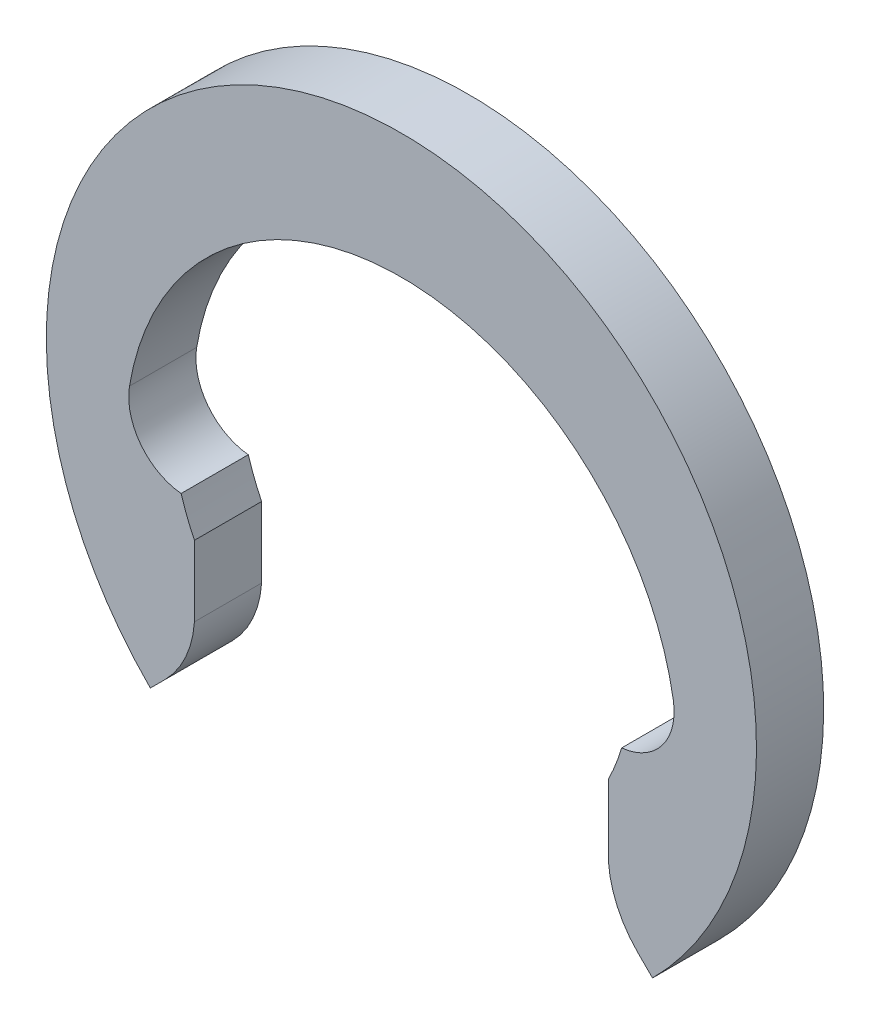
SolidWorks part; units mm, degrees
ref_plane "Front" through (0, 0, 0) normal (0, 0, 1) x (1, 0, 0)
ref_plane "Top" through (0, 0, 0) normal (0, 1, 0) x (1, 0, 0)
ref_plane "Right" through (0, 0, 0) normal (1, 0, 0) x (0, 0, -1)
sketch "Layout" plane through (0, 0, 0) normal (0, 0, 1) x (1, 0, 0)
  line L0 (0, 3.7) -> (0, -3.7) construction
  line L1 (-2.4, 0) -> (-2.8333, 0) construction
  line L2 (-3.7, 0) -> (-4.4, 0) construction
  line L3 (-2.4, 0) -> (2.4, 0) construction
  line L4 (-2.1567, -2.1567) -> (-2.1567, -1.053) construction
  line L5 (-2.2956, -0.7) -> (2.2956, -0.7) construction
  line L6 (-2.4, 0) -> (-2.4, -0.7) construction
  line L7 (0, 0) -> (-1.6971, -1.6971) construction
  line L8 (-1.6971, -1.6971) -> (-2.6163, -2.6163) construction
  line L9 (-2.8333, 0) -> (-3.2667, 0) construction
  line L10 (-3.2667, 0) -> (-3.7, 0) construction
  circle A0 centre (0, 0) radius 3.7 construction
  circle A1 centre (0, 0) radius 2.4 construction
  arc A2 (0, 2.4) -> (-2.8333, 0) centre (0, -0.4725) ccw construction
  circle A3 centre (0, 0) radius 3.8 construction
  arc A4 (-2.8333, 0) -> (-2.2956, -0.7) centre (-2.2381, -0.0993) ccw construction
  dimension "D1" = 45
sketch "Sketch2" plane through (0, 0, 0) normal (0, 0, 1) x (1, 0, 0)
  line L0 (-2.1567, -2.1567) -> (-2.1567, -1.7888) construction
  line L1 (-2.1567, -1.7888) -> (-2.1567, -1.4209)
  line L2 (-2.1567, -1.4209) -> (-2.1567, -1.053)
  line L4 (0, 3.7) -> (0, -3.7) construction
  line L5 (-2.1567, -2.1567) -> (-2.3099, -2.3099) construction
  line L6 (0, 3.7) -> (0, 2.4) construction
  line L7 (-2.3099, -2.3099) -> (-2.4631, -2.4631) construction
  line L8 (-2.4631, -2.4631) -> (-2.6163, -2.6163)
  line L9 (-1.6971, -1.6971) -> (-2.6163, -2.6163) construction
  line L10 (2.1567, -1.4209) -> (2.1567, -1.053)
  line L11 (2.1567, -1.7888) -> (2.1567, -1.4209)
  line L12 (2.4631, -2.4631) -> (2.6163, -2.6163)
  circle A0 centre (0, 0) radius 3.7 construction
  arc A1 (0, 2.4) -> (-2.8333, 0) centre (0, -0.4725) ccw construction
  arc A2 (-2.8333, 0) -> (-2.2956, -0.7) centre (-2.2381, -0.0993) ccw construction
  circle A3 centre (0, 0) radius 2.4 construction
  arc A4 (2.6163, -2.6163) -> (-2.6163, -2.6163) centre (0, 0) ccw
  arc A5 (2.8333, 0) -> (-2.8333, 0) centre (0, -0.4725) ccw
  arc A6 (-2.8333, 0) -> (-2.2956, -0.7) centre (-2.2381, -0.0993) ccw
  arc A7 (-2.2956, -0.7) -> (-2.1567, -1.053) centre (0, 0) ccw
  arc A8 (-2.1567, -1.7888) -> (-2.4631, -2.4631) centre (-3.2087, -1.7175) cw
  arc A9 (2.1567, -1.7888) -> (2.4631, -2.4631) centre (3.2087, -1.7175) ccw
  arc A10 (2.2956, -0.7) -> (2.1567, -1.053) centre (0, 0) cw
  arc A11 (2.8333, 0) -> (2.2956, -0.7) centre (2.2381, -0.0993) cw
extrude "Boss-Extrude1" add sketch "Sketch2" along normal blind 0.7
equation "\"D1@Boss-Extrude1\"=\"thickness@Layout\""
